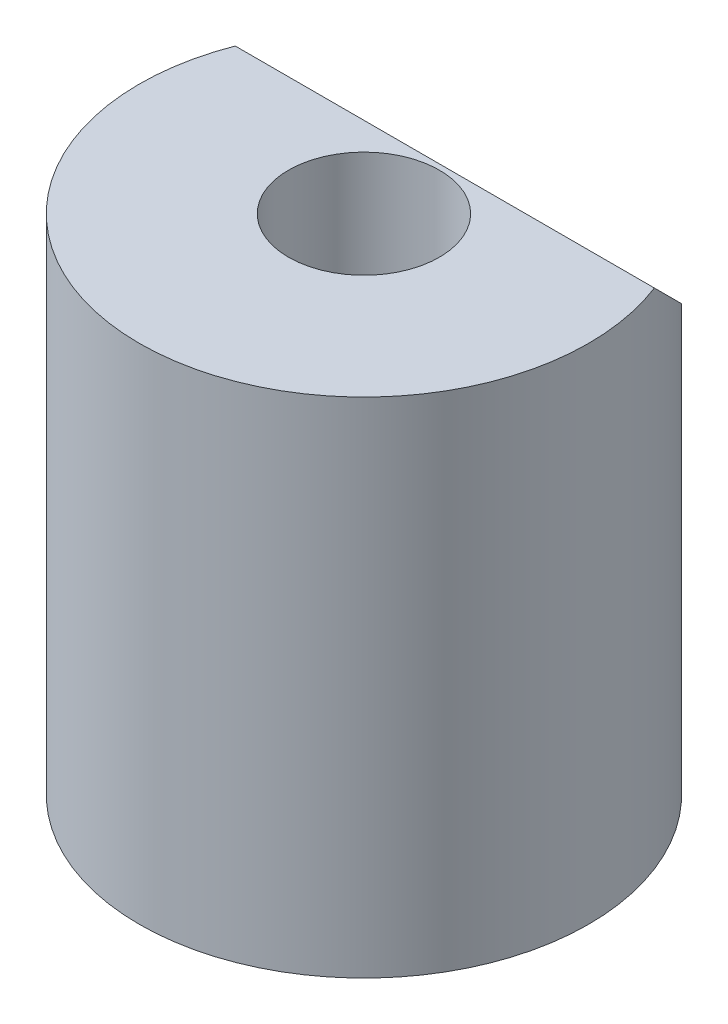
SolidWorks part; units mm, degrees
ref_plane "Front Plane" through (0, 0, 0) normal (0, 0, 1) x (1, 0, 0)
ref_plane "Top Plane" through (0, 0, 0) normal (0, 1, 0) x (1, 0, 0)
ref_plane "Right Plane" through (0, 0, 0) normal (1, 0, 0) x (0, 0, -1)
sketch "Sketch1" plane through (0, 0, 0) normal (0, 1, 0) x (1, 0, 0)
  circle A0 centre (0, 0) radius 6.25
  dimension "D1" = 12.5
extrude "Boss-Extrude1" add sketch "Sketch1" along normal blind 14
sketch "Sketch2" plane through (0, 14, 0) normal (0, 1, 0) x (1, 0, 0)
  circle A0 centre (0, 0) radius 2.1
  dimension "D1" = 4.2
extrude "Cut-Extrude1" cut sketch "Sketch2" against normal blind 12
ref_plane "Plane1" through (0, 0, 0) normal (1, 0, 0) x (0, 0, -1)
sketch "Sketch3" plane through (0, 0, 0) normal (1, 0, 0) x (0, 0, -1)
  line L0 (2.25, 14) -> (6.25, 10)
  line L1 (6.25, 0) -> (6.25, 14) construction
  line L2 (6.25, 14) -> (-6.25, 14) construction
  line L3 (6.25, 10) -> (6.25, 14)
  line L4 (6.25, 14) -> (2.25, 14)
  dimension "D1" = 45
  dimension "4" = 4
extrude "Cut-Extrude2" cut sketch "Sketch3" against normal mid plane 14
